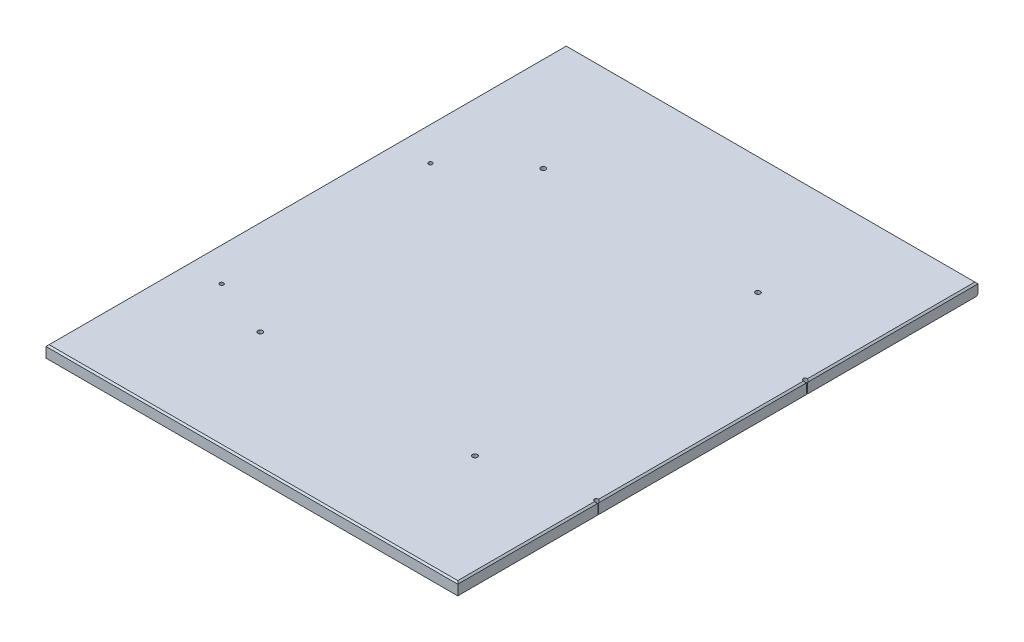
SolidWorks part; units mm, degrees
material "Oak"
ref_plane "Front Plane" through (0, 0, 0) normal (0, 0, 1) x (1, 0, 0)
ref_plane "Top Plane" through (0, 0, 0) normal (0, 1, 0) x (1, 0, 0)
ref_plane "Right Plane" through (0, 0, 0) normal (1, 0, 0) x (0, 0, -1)
sketch "Sketch1" plane through (0, 0, 0) normal (0, 1, 0) x (1, 0, 0)
  line L1 (0, 0) -> (669.8488, 0)
  line L2 (0, 0) -> (0, 846.328)
  line L3 (0, 846.328) -> (669.8488, 846.328)
  line L4 (669.8488, 0) -> (669.8488, 846.328)
  dimension "D1" = 846.328
  dimension "D2" = 669.8488
extrude "Boss-Extrude1" add sketch "Sketch1" along normal blind 19.05
chamfer "Chamfer1" distance 2.54 angle 45 4 edges at (334.9244, 19.05, -846.328) (669.8488, 19.05, -423.164) (334.9244, 19.05, 0) (0, 19.05, -423.164)
chamfer "Chamfer2" distance 2.54 angle 45 1 edges at (334.9244, 0, -846.328)
sketch "Sketch3" plane through (0, 19.05, 0) normal (0, 1, 0) x (1, 0, 0)
  circle A1 centre (505.5807, 192.2835) radius 3.9688
  circle A3 centre (156.3307, 192.2835) radius 3.9687
  circle A5 centre (156.3306, 652.6585) radius 3.9687
  circle A7 centre (505.5807, 652.6585) radius 3.9688
  dimension "D5" = 7.9375
  dimension "D1" = 156.3307
  dimension "D2" = 192.2835
  dimension "D3" = 349.25
  dimension "D4" = 460.375
extrude "Cut-Extrude4" cut sketch "Sketch3" against normal through all
sketch "Sketch2" plane through (0, 19.05, 0) normal (0, 1, 0) x (1, 0, 0)
  line L1 (57.15, 568.325) -> (666.75, 568.325) construction
  line L2 (57.15, 568.325) -> (57.15, 228.6) construction
  line L3 (57.15, 228.6) -> (666.75, 228.6) construction
  line L4 (666.75, 568.325) -> (666.75, 228.6) construction
  circle A1 centre (57.15, 568.325) radius 3.175
  circle A3 centre (57.15, 228.6) radius 3.175
  circle A5 centre (666.75, 568.325) radius 3.175
  circle A7 centre (666.75, 228.6) radius 3.175
  dimension "D1" = 6.35
  dimension "D2" = 609.6
  dimension "D3" = 339.725
  dimension "D4" = 228.6
  dimension "D5" = 57.15
extrude "Cut-Extrude3" cut sketch "Sketch2" against normal through all
